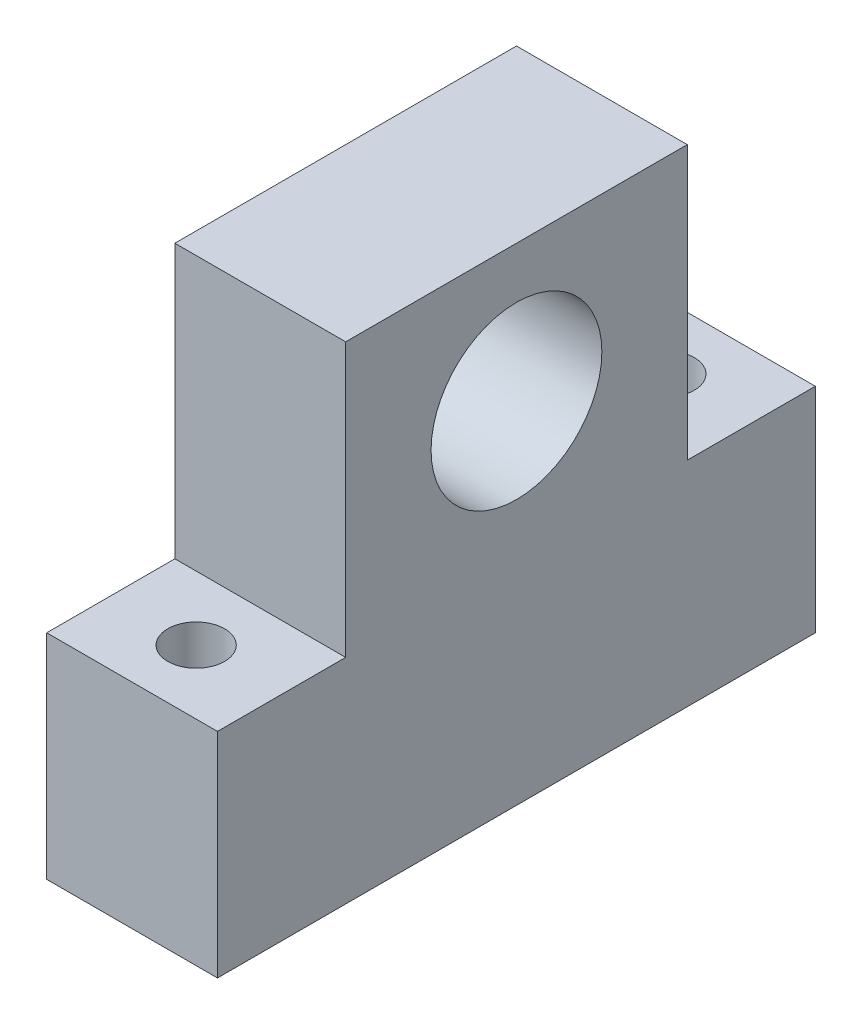
SolidWorks part; units mm, degrees
ref_plane "Front Plane" through (0, 0, 0) normal (0, 0, 1) x (1, 0, 0)
ref_plane "Top Plane" through (0, 0, 0) normal (0, 1, 0) x (1, 0, 0)
ref_plane "Right Plane" through (0, 0, 0) normal (1, 0, 0) x (0, 0, -1)
sketch "Sketch2" plane through (0, 0, 0) normal (0, 1, 0) x (1, 0, 0)
  line L1 (0, 0) -> (12.7, 0)
  line L2 (0, 0) -> (0, 44.45)
  line L3 (0, 44.45) -> (12.7, 44.45)
  line L4 (12.7, 0) -> (12.7, 44.45)
extrude "Boss-Extrude1" add sketch "Sketch2" along normal blind 15.88
sketch "Sketch4" plane through (0, 15.88, 0) normal (0, 1, 0) x (1, 0, 0)
  line L0 (12.7, 0) -> (12.7, 44.45) construction
  line L1 (12.7, 34.93) -> (0, 34.93)
  line L2 (12.7, 34.93) -> (12.7, 9.53)
  line L3 (12.7, 9.53) -> (0, 9.53)
  line L4 (0, 34.93) -> (0, 9.53)
  line L5 (0, 44.45) -> (0, 0) construction
extrude "Boss-Extrude2" add sketch "Sketch4" along normal blind 20.32
sketch "Sketch5" plane through (12.7, 0, 0) normal (1, 0, 0) x (0, 0, -1)
  circle A0 centre (22.23, 26.04) radius 6.35
extrude "Cut-Extrude1" cut sketch "Sketch5" against normal blind 12.7
sketch "Sketch6" plane through (0, 15.88, 0) normal (0, 1, 0) x (1, 0, 0)
  circle A0 centre (6.35, 39.69) radius 2.11
extrude "Cut-Extrude2" cut sketch "Sketch6" against normal blind 20.7
sketch "Sketch7" plane through (0, 15.88, 0) normal (0, 1, 0) x (1, 0, 0)
  circle A0 centre (6.35, 4.765) radius 2.11
extrude "Cut-Extrude3" cut sketch "Sketch7" against normal blind 16.7
